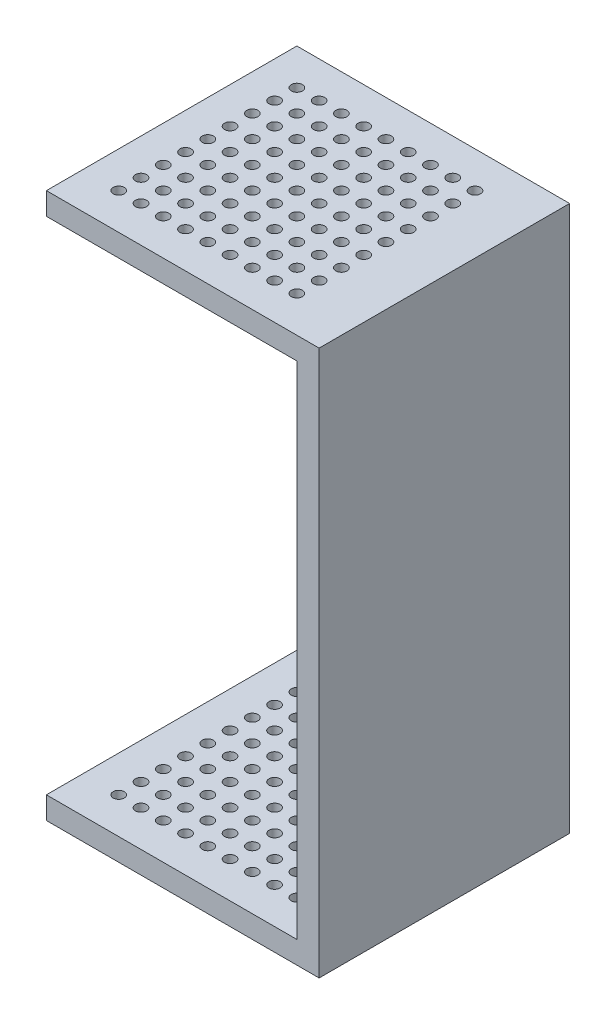
SolidWorks part; units mm, degrees
ref_plane "Front Plane" through (0, 0, 0) normal (0, 0, 1) x (1, 0, 0)
ref_plane "Top Plane" through (0, 0, 0) normal (0, 1, 0) x (1, 0, 0)
ref_plane "Right Plane" through (0, 0, 0) normal (1, 0, 0) x (0, 0, -1)
sketch "Sketch1" plane through (0, 0, 0) normal (0, 1, 0) x (1, 0, 0)
  line L1 (12.25, -11.25) -> (-12.25, -11.25)
  line L2 (12.25, -11.25) -> (12.25, 11.25)
  line L3 (12.25, 11.25) -> (-12.25, 11.25)
  line L4 (-12.25, -11.25) -> (-12.25, 11.25)
  line L5 (12.25, -11.25) -> (-12.25, 11.25) construction
  line L6 (12.25, 11.25) -> (-12.25, -11.25) construction
  point P0 (0, 0)
  dimension "D1" = 24.5
  dimension "D2" = 22.5
extrude "Boss-Extrude1" add sketch "Sketch1" along normal blind 2
sketch "Sketch2" plane through (0, 2, 0) normal (0, 1, 0) x (1, 0, 0)
  line L0 (-12.25, 11.25) -> (12.25, -11.25) construction
  line L1 (12.25, 11.25) -> (-12.25, -11.25) construction
  line L3 (12.25, 11.25) -> (-12.25, 11.25) construction
  line L5 (12.25, -11.25) -> (10.25, -11.25)
  line L7 (10.25, -11.25) -> (10.25, 11.25)
  line L8 (10.25, 11.25) -> (12.25, 11.25)
  line L9 (-12.25, -11.25) -> (12.25, -11.25) construction
  line L12 (12.25, 11.25) -> (12.25, -11.25)
  dimension "D2" = 2
extrude "Boss-Extrude2" add sketch "Sketch2" along normal blind 45
sketch "Sketch3" plane through (0, 0, 0) normal (0, -1, 0) x (1, 0, 0)
  line L0 (-9, 8) -> (-9, 11.25) construction
  line L1 (12.25, 11.25) -> (-12.25, -11.25) construction
  line L2 (-12.25, -11.25) -> (-12.25, 11.25) construction
  line L7 (-12.25, 11.25) -> (12.25, 11.25) construction
  circle A0 centre (-9, 8) radius 0.5
  circle A1 centre (-7, 8) radius 0.5
  circle A2 centre (-5, 8) radius 0.5
  circle A3 centre (-3, 8) radius 0.5
  circle A4 centre (-1, 8) radius 0.5
  circle A5 centre (1, 8) radius 0.5
  circle A6 centre (3, 8) radius 0.5
  circle A7 centre (5, 8) radius 0.5
  circle A8 centre (7, 8) radius 0.5
  circle A9 centre (-7, 6) radius 0.5
  circle A10 centre (-5, 6) radius 0.5
  circle A11 centre (-3, 6) radius 0.5
  circle A12 centre (-1, 6) radius 0.5
  circle A13 centre (1, 6) radius 0.5
  circle A14 centre (3, 6) radius 0.5
  circle A15 centre (5, 6) radius 0.5
  circle A16 centre (7, 6) radius 0.5
  circle A17 centre (-7, 4) radius 0.5
  circle A18 centre (-5, 4) radius 0.5
  circle A19 centre (-3, 4) radius 0.5
  circle A20 centre (-1, 4) radius 0.5
  circle A21 centre (1, 4) radius 0.5
  circle A22 centre (3, 4) radius 0.5
  circle A23 centre (5, 4) radius 0.5
  circle A24 centre (7, 4) radius 0.5
  circle A25 centre (-7, 2) radius 0.5
  circle A26 centre (-5, 2) radius 0.5
  circle A27 centre (-3, 2) radius 0.5
  circle A28 centre (-1, 2) radius 0.5
  circle A29 centre (1, 2) radius 0.5
  circle A30 centre (3, 2) radius 0.5
  circle A31 centre (5, 2) radius 0.5
  circle A32 centre (7, 2) radius 0.5
  circle A33 centre (-7, 0) radius 0.5
  circle A34 centre (-5, 0) radius 0.5
  circle A35 centre (-3, 0) radius 0.5
  circle A36 centre (-1, 0) radius 0.5
  circle A37 centre (1, 0) radius 0.5
  circle A38 centre (3, 0) radius 0.5
  circle A39 centre (5, 0) radius 0.5
  circle A40 centre (7, 0) radius 0.5
  circle A41 centre (-7, -2) radius 0.5
  circle A42 centre (-5, -2) radius 0.5
  circle A43 centre (-3, -2) radius 0.5
  circle A44 centre (-1, -2) radius 0.5
  circle A45 centre (1, -2) radius 0.5
  circle A46 centre (3, -2) radius 0.5
  circle A47 centre (5, -2) radius 0.5
  circle A48 centre (7, -2) radius 0.5
  circle A49 centre (-7, -4) radius 0.5
  circle A50 centre (-5, -4) radius 0.5
  circle A51 centre (-3, -4) radius 0.5
  circle A52 centre (-1, -4) radius 0.5
  circle A53 centre (1, -4) radius 0.5
  circle A54 centre (3, -4) radius 0.5
  circle A55 centre (5, -4) radius 0.5
  circle A56 centre (7, -4) radius 0.5
  circle A57 centre (-7, -6) radius 0.5
  circle A58 centre (-5, -6) radius 0.5
  circle A59 centre (-3, -6) radius 0.5
  circle A60 centre (-1, -6) radius 0.5
  circle A61 centre (1, -6) radius 0.5
  circle A62 centre (3, -6) radius 0.5
  circle A63 centre (5, -6) radius 0.5
  circle A64 centre (7, -6) radius 0.5
  circle A65 centre (-7, -8) radius 0.5
  circle A66 centre (-5, -8) radius 0.5
  circle A67 centre (-3, -8) radius 0.5
  circle A68 centre (-1, -8) radius 0.5
  circle A69 centre (1, -8) radius 0.5
  circle A70 centre (3, -8) radius 0.5
  circle A71 centre (5, -8) radius 0.5
  circle A72 centre (7, -8) radius 0.5
  circle A73 centre (-9, 6) radius 0.5
  circle A74 centre (-9, 4) radius 0.5
  circle A75 centre (-9, 2) radius 0.5
  circle A76 centre (-9, 0) radius 0.5
  circle A77 centre (-9, -2) radius 0.5
  circle A78 centre (-9, -4) radius 0.5
  circle A79 centre (-9, -6) radius 0.5
  circle A80 centre (-9, -8) radius 0.5
  dimension "D1" = 1
  dimension "D2" = 9
  dimension "D3" = 3.25
  dimension "D4" = 3.25
  dimension "D5" = 9
sketch "Sketch4" plane through (0, 47, 0) normal (0, 1, 0) x (1, 0, 0)
  line L1 (-12.25, 11.25) -> (12.25, 11.25)
  line L2 (-12.25, 11.25) -> (-12.25, -11.25)
  line L3 (-12.25, -11.25) -> (12.25, -11.25)
  line L4 (12.25, 11.25) -> (12.25, -11.25)
  line L5 (-12.25, 11.25) -> (12.25, -11.25) construction
  line L6 (-12.25, -11.25) -> (12.25, 11.25) construction
  point P0 (0, 0)
  dimension "D1" = 24.5
  dimension "D2" = 22.5
extrude "Boss-Extrude3" add sketch "Sketch4" along normal blind 2
extrude "Cut-Extrude1" cut sketch "Sketch3" against normal through all
equation "\"D1@Sketch1\"=\"D2@Sketch1\"+2"
equation "\"D1@Sketch4\"=\"D2@Sketch4\"+2"
equation "\"D3@Sketch3\"=\"D4@Sketch3\""
